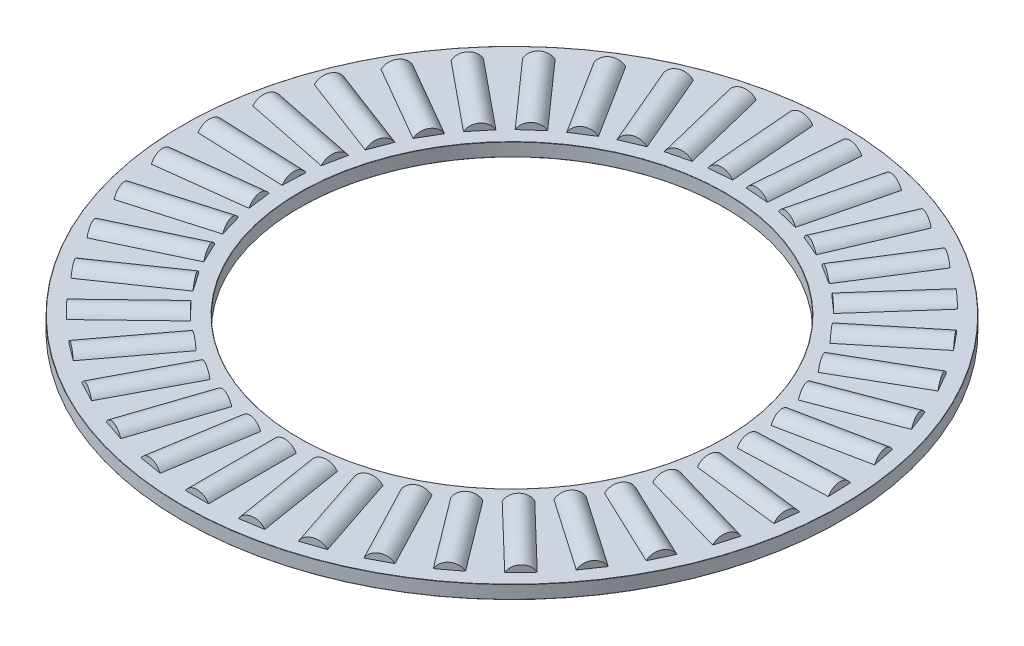
SolidWorks part; units mm, degrees
ref_plane "Front Plane" through (0, 0, 0) normal (0, 0, 1) x (1, 0, 0)
ref_plane "Top Plane" through (0, 0, 0) normal (0, 1, 0) x (1, 0, 0)
ref_plane "Right Plane" through (0, 0, 0) normal (1, 0, 0) x (0, 0, -1)
sketch "Sketch1" plane through (0, 0, 0) normal (1, 0, 0) x (0, 0, -1)
  line L0 (-24.6062, 0) -> (24.6062, 0) construction
  line L1 (0, -0.9922) -> (0, 0.9922) construction
  line L2 (-24.6062, 0.4961) -> (-15.875, 0.4961)
  line L3 (-24.6062, 0.4961) -> (-24.6062, -0.4961)
  line L4 (-24.6062, -0.4961) -> (-15.875, -0.4961)
  line L5 (-15.875, 0.4961) -> (-15.875, -0.4961)
  line L7 (-20.2406, 0.9922) -> (-20.2406, 0.4961) construction
  line L8 (-23.5148, 0.9922) -> (-16.9664, 0.9922) construction
  line L9 (-23.5148, 0.9922) -> (-23.5148, -0.9922) construction
  line L10 (-23.5148, -0.9922) -> (-16.9664, -0.9922) construction
  line L11 (-16.9664, 0.9922) -> (-16.9664, -0.9922) construction
  point P16 (-23.5148, 0)
  dimension "D1" = 6.5484
  dimension "OD" = 49.2125
  dimension "Shaft Dia" = 31.75
  dimension "Th" = 1.9844
  dimension "D2" = 0.9922
  dimension "D3" = 8.7312
revolve "Revolve1" add sketch "Sketch1" angle 360 about L1
sketch "Sketch3" plane through (0, 0, 0) normal (1, 0, 0) x (0, 0, -1)
  line L0 (-23.5148, 0.9922) -> (-23.5148, -0.9922) construction
  line L1 (-23.5148, 0) -> (-16.9664, 0)
  line L2 (-23.5148, 0) -> (-23.5148, 0.9922)
  line L3 (-23.5148, 0.9922) -> (-16.9664, 0.9922)
  line L4 (-16.9664, 0) -> (-16.9664, 0.9922)
revolve "Cut-Revolve1" cut sketch "Sketch3" angle 360 about L1
sketch "Sketch2" plane through (0, 0, 0) normal (1, 0, 0) x (0, 0, -1)
  line L1 (-23.5148, 0) -> (-16.9664, 0)
  line L2 (-23.5148, 0) -> (-23.5148, 0.9922)
  line L3 (-23.5148, 0.9922) -> (-16.9664, 0.9922)
  line L4 (-16.9664, 0) -> (-16.9664, 0.9922)
revolve "Revolve2" add sketch "Sketch2" angle 360 about L1
ref_axis "Axis1" through (0, 0.9922, 0) along (0, -1, 0)
pattern_circular "CirPattern1" count 39 every 9.231 about axis through (0, 0.9922, 0) along (0, -1, 0) of bodies 187 411
pattern_circular "CirPattern2" count 39 every 9.231 about axis through (0, 0, 0) along (0, 1, 0) of "Cut-Revolve1"
sketch "Sketch4" plane through (0, 0, 0) normal (1, 0, 0) x (0, 0, -1)
  line L0 (-24.6062, 0.4961) -> (-24.6062, -0.4961) construction
  line L1 (-24.6062, 9.1091) -> (-15.875, 9.1091)
  line L2 (-24.6062, 9.1091) -> (-24.6063, 9.9219)
  line L3 (-24.6063, 9.9219) -> (-15.875, 9.9219)
  line L4 (-15.875, 9.1091) -> (-15.875, 9.9219)
  line L5 (-24.6062, -9.9219) -> (-15.875, -9.9219)
  line L6 (-24.6062, -9.9219) -> (-24.6062, -9.1091)
  line L7 (-24.6062, -9.1091) -> (-15.875, -9.1091)
  line L8 (-15.875, -9.9219) -> (-15.875, -9.1091)
  line L10 (-15.875, 0.4961) -> (-15.875, -0.4961) construction
  line L11 (0, 0) -> (-24.6062, 0) construction
  line L12 (-24.6062, 0) -> (24.6062, 0) construction
  line L13 (0, -0.9922) -> (0, 0.9922) construction
  dimension "Ht" = 19.8438
  dimension "Washer Th" = 0.8128
  dimension "Washer ID" = 31.75
  dimension "Washer OD" = 49.2125
revolve "Revolve3" [suppressed] add sketch "Sketch4" angle 360 about L1
fillet "Fillet1" [suppressed] radius 0.0198
fillet "Fillet2" radius 0.0198 4 edges at (0, -0.4961, -15.875) (0, 0.4961, -15.875) (0, -0.4961, -24.6062) (0, 0.4961, -24.6062)
fillet "Fillet3" [suppressed] radius 0.0198
equation "\"D2@Sketch1\" = \"Th@Sketch1\"*.5"
equation "\"D1@Fillet1\" = \"Th@Sketch1\"*.01"
equation "\"D1@Fillet2\" = \"D1@Fillet1\""
equation "\"D1@Fillet3\" = \"D1@Fillet1\""
equation "\"D1@Sketch1\" = \"D3@Sketch1\"*.75"
equation "\"Angle@CirPattern1\" = 360/\"Rollers@CirPattern1\""
equation "\"Rollers@CirPattern1\" = \"OD@Sketch1\"*20"
equation "\"D1@CirPattern2\" = \"Rollers@CirPattern1\""
equation "\"D2@CirPattern2\" = \"Angle@CirPattern1\""
equation "\"Ht@Sketch4\" = \"Th@Sketch1\"*10"
